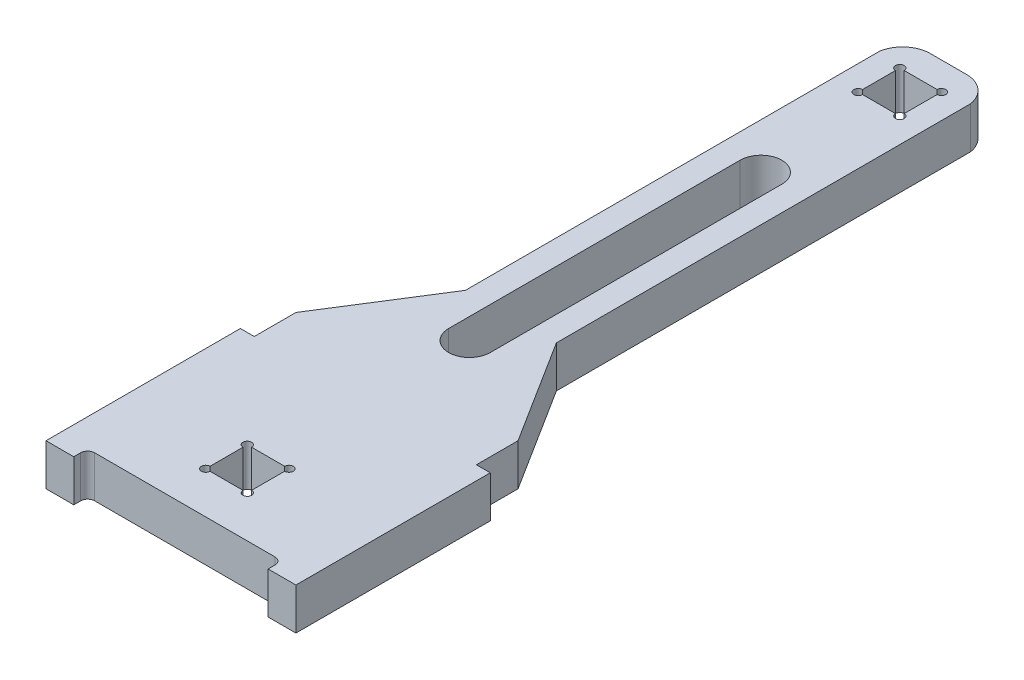
SolidWorks part; units mm, degrees
ref_plane "Front" through (0, 0, 0) normal (0, 0, 1) x (1, 0, 0)
ref_plane "Top" through (0, 0, 0) normal (0, 1, 0) x (1, 0, 0)
ref_plane "Right" through (0, 0, 0) normal (1, 0, 0) x (0, 0, -1)
other "Center of Mass"
sketch "Sketch1" plane through (0, 0, 0) normal (0, 1, 0) x (1, 0, 0)
  line L0 (-4.1386, 94.6093) -> (4.1386, 94.6093)
  line L1 (-10.4032, 89.2968) -> (-10.4032, -5.4484)
  line L2 (-10.4032, -5.4484) -> (-25.4, -29.2157)
  line L3 (28.575, -38.7407) -> (28.575, -83.1907)
  line L4 (28.575, -83.1907) -> (-28.575, -83.1907)
  line L5 (-28.575, -83.1907) -> (-28.575, -38.7407)
  line L6 (-25.4, -38.7407) -> (-28.575, -38.7407)
  line L7 (-25.4, -29.2157) -> (-25.4, -38.7407)
  line L8 (25.4, -38.7407) -> (25.4, -29.2157)
  line L9 (25.4, -38.7407) -> (28.575, -38.7407)
  line L10 (25.4, -29.2157) -> (10.4032, -5.4484)
  line L11 (-4.7625, -60.9657) -> (4.7625, -60.9657)
  line L12 (-4.7625, -60.9657) -> (-4.7625, -70.4907)
  line L13 (-4.7625, -70.4907) -> (4.7625, -70.4907)
  line L14 (4.7625, -60.9657) -> (4.7625, -70.4907)
  line L15 (-4.7625, -60.9657) -> (4.7625, -70.4907) construction
  line L16 (-4.7625, -70.4907) -> (4.7625, -60.9657) construction
  line L17 (-4.7625, 88.2593) -> (4.7625, 88.2593)
  line L18 (-4.7625, 88.2593) -> (-4.7625, 78.7343)
  line L19 (-4.7625, 78.7343) -> (4.7625, 78.7343)
  line L20 (4.7625, 88.2593) -> (4.7625, 78.7343)
  line L21 (-4.7625, 88.2593) -> (4.7625, 78.7343) construction
  line L22 (-4.7625, 78.7343) -> (4.7625, 88.2593) construction
  line L23 (10.4032, -5.4484) -> (10.4032, 89.2968)
  arc A0 (4.1386, 94.6093) -> (10.4032, 89.2968) centre (4.1386, 88.2593) cw
  arc A1 (-4.1386, 94.6093) -> (-10.4032, 89.2968) centre (-4.1386, 88.2593) ccw
  point P7 (0, -83.1907)
  point P9 (0, 94.6093)
  point P18 (0, 83.4968)
  point P23 (0, -65.7282)
  dimension "D2" = 6.35
  dimension "D1" = 57.15
  dimension "D3" = 177.8
  dimension "D4" = 9.525
  dimension "D5" = 22.225
  dimension "D6" = 50.8
  dimension "D7" = 9.525
  dimension "D8" = 6.35
  dimension "D9" = 12.7
  dimension "D10" = 9.525
extrude "Boss-Extrude1" add sketch "Sketch1" along normal blind 9.525
sketch "Sketch4" plane through (0, 9.525, 0) normal (0, 1, 0) x (1, 0, 0)
  line L0 (0, 51.7468) -> (0, -14.9282) construction
  line L1 (4.7625, 51.7468) -> (4.7625, -14.9282)
  line L2 (-4.7625, 51.7468) -> (-4.7625, -14.9282)
  line L3 (-28.575, -83.1907) -> (28.575, -83.1907) construction
  arc A0 (4.7625, 51.7468) -> (-4.7625, 51.7468) centre (0, 51.7468) ccw
  arc A1 (-4.7625, -14.9282) -> (4.7625, -14.9282) centre (0, -14.9282) ccw
  point P2 (0, 18.4093)
  dimension "D2" = 76.2
  dimension "D1" = 9.525
  dimension "D3" = 101.6
ref_plane "Plane1" through (0, 0, -5.7093) normal (0, 0, -1) x (-1, 0, 0)
extrude "Cut-Extrude2" cut sketch "Sketch4" against normal through all
sketch "Sketch5" plane through (0, 9.525, 0) normal (0, 1, 0) x (1, 0, 0)
  line L0 (-28.575, -83.1907) -> (28.575, -83.1907) construction
  line L1 (-22.225, -83.1907) -> (22.225, -83.1907)
  line L2 (-22.225, -83.1907) -> (-22.225, -81.6032)
  line L3 (-20.6375, -80.0157) -> (20.6375, -80.0157)
  line L4 (22.225, -83.1907) -> (22.225, -81.6032)
  line L5 (-28.575, -38.7407) -> (-28.575, -83.1907) construction
  arc A0 (20.6375, -80.0157) -> (22.225, -81.6032) centre (20.6375, -81.6032) cw
  arc A1 (-22.225, -81.6032) -> (-20.6375, -80.0157) centre (-20.6375, -81.6032) cw
  point P6 (0, -80.0157)
  point P14 (-22.225, -80.0157)
  dimension "D3" = 1.5875
  dimension "D1" = 3.175
  dimension "D2" = 6.35
extrude "Cut-Extrude3" cut sketch "Sketch5" against normal through all
hole_wizard "5/64 (0.07813) Diameter Hole1" positions "Sketch9" profile "Sketch10" hole size "5/64" standard "ANSI Inch" end condition through all
sketch "Sketch9" plane through (0, 9.525, 0) normal (0, 1, 0) x (1, 0, 0)
  line L0 (-4.7625, -70.4907) -> (4.7625, -70.4907) construction
  line L1 (-4.7625, -60.9657) -> (-4.7625, -70.4907) construction
  point P0 (-4.7625, 88.2593)
  point P3 (4.7625, 88.2593)
  point P6 (4.7625, 78.7343)
  point P9 (-4.7625, 78.7343)
  point P12 (-4.7625, -60.9657)
  point P15 (4.7625, -60.9657)
  point P18 (4.7625, -70.4907)
  point P21 (-4.7625, -70.4907)
sketch "Sketch10" plane through (-4.7625, 9.525, -88.2593) normal (1, 0, 0) x (0, 0, 1)
  line L0 (0, 0) -> (0, 9.525)
  line L1 (0, 9.525) -> (0.9923, 9.525)
  line L2 (0.9923, 9.525) -> (0.9923, 0)
  line L5 (0.9923, 0) -> (0, 0)
  line L11 (0, -6.35) -> (0, 107.95) construction
  dimension "Thru Hole Dia." = 1.9845
  dimension "Thru Hole Depth" = 9.525
sketch "Sketch13" [suppressed] plane through (0, 0, 0) normal (0, 1, 0) x (1, 0, 0)
  line L0 (-38.227, 104.2613) -> (38.227, 104.2613)
  line L1 (-31.877, 97.9113) -> (31.877, 97.9113)
  line L2 (-31.877, 97.9113) -> (-31.877, -97.9113)
  line L3 (-31.877, -97.9113) -> (31.877, -97.9113)
  line L4 (31.877, 97.9113) -> (31.877, -97.9113)
  line L5 (-31.877, 97.9113) -> (31.877, -97.9113) construction
  line L6 (-31.877, -97.9113) -> (31.877, 97.9113) construction
  line L7 (38.227, 104.2613) -> (38.227, -104.2613)
  line L8 (-38.227, -104.2613) -> (38.227, -104.2613)
  line L9 (-38.227, 104.2613) -> (-38.227, -104.2613)
  line L11 (-28.575, -38.7407) -> (-28.575, -83.1907) construction
  line L14 (4.1386, 94.6093) -> (-4.1386, 94.6093) construction
  point P0 (0, 0)
  dimension "D2" = 3.302
  dimension "D3" = 3.302
  dimension "D1" = 6.35
extrude "Boss-Extrude7" [suppressed] add sketch "Sketch13" along normal blind 9.525
sketch "Sketch6" [suppressed] plane through (-10.4032, 0, 0) normal (1, 0, 0) x (0, 0, -1)
  line L0 (89.2968, 9.525) -> (89.2968, 0) construction
  circle A0 centre (72.2968, 4.7625) radius 1.5875
  circle A1 centre (21.4968, 4.7625) radius 1.5875
  point P4 (89.2968, 4.7625)
  dimension "D1" = 3.175
  dimension "D3" = 50.8
  dimension "D2" = 17
extrude "Boss-Extrude2" [suppressed] add sketch "Sketch6" against normal up to next
sketch "Sketch7" [suppressed] plane through (28.575, 0, 0) normal (1, 0, 0) x (0, 0, -1)
  line L0 (-83.1907, 9.525) -> (-83.1907, 0) construction
  line L3 (-83.1907, 9.525) -> (-38.7407, 9.525) construction
  circle A0 centre (-60.9657, 4.7625) radius 1.5875
  point P5 (-83.1907, 4.7625)
  point P8 (-60.9657, 9.525)
  dimension "D1" = 3.175
extrude "Boss-Extrude3" [suppressed] add sketch "Sketch7" along normal up to next
sketch "Sketch8" [suppressed] plane through (0, 0, 80.0157) normal (0, 0, 1) x (1, 0, 0)
  line L0 (-20.6375, 0) -> (-20.6375, 9.525) construction
  line L1 (20.6375, 9.525) -> (-20.6375, 9.525) construction
  circle A0 centre (0, 4.7625) radius 1.5875
  point P6 (-20.6375, 4.7625)
  point P9 (0, 9.525)
  dimension "D1" = 3.175
extrude "Boss-Extrude4" [suppressed] add sketch "Sketch8" along normal up to next
sketch "Sketch11" [suppressed] plane through (0, 0, -94.6093) normal (0, 0, -1) x (-1, 0, 0)
  line L0 (-4.1386, 9.525) -> (-4.1386, 0) construction
  circle A0 centre (0, 4.7625) radius 1.5875
  point P4 (-4.1386, 4.7625)
  dimension "D1" = 3.175
extrude "Boss-Extrude5" [suppressed] add sketch "Sketch11" along normal up to next contours A0
sketch "Sketch12" [suppressed] plane through (4.9819, 0, -3.1435) normal (0.8457, 0, -0.5336) x (-0.5336, 0, -0.8457)
  line L0 (-38.2625, 0) -> (-10.1593, 0) construction
  line L1 (-10.1593, 9.525) -> (-10.1593, 0) construction
  circle A0 centre (-24.2109, 4.7625) radius 1.5875
  point P4 (-24.2109, 0)
  point P7 (-10.1593, 4.7625)
  dimension "D1" = 3.175
extrude "Boss-Extrude6" [suppressed] add sketch "Sketch12" along normal up to next
sketch "Sketch15" [suppressed] plane through (-4.9819, 0, -3.1435) normal (-0.8457, 0, -0.5336) x (-0.5336, 0, 0.8457)
  line L0 (10.1593, 9.525) -> (38.2625, 9.525) construction
  line L1 (10.1593, 9.525) -> (10.1593, 0) construction
  circle A0 centre (24.2109, 4.7625) radius 2.0617
  point P4 (24.2109, 9.525)
  point P7 (10.1593, 4.7625)
extrude "Boss-Extrude8" [suppressed] add sketch "Sketch15" along normal up to next
mirror "Mirror8" [suppressed] about plane through (0, 0, 0) normal (1, 0, 0)
mirror "Mirror7" [suppressed] about plane through (0, 0, 0) normal (1, 0, 0)
